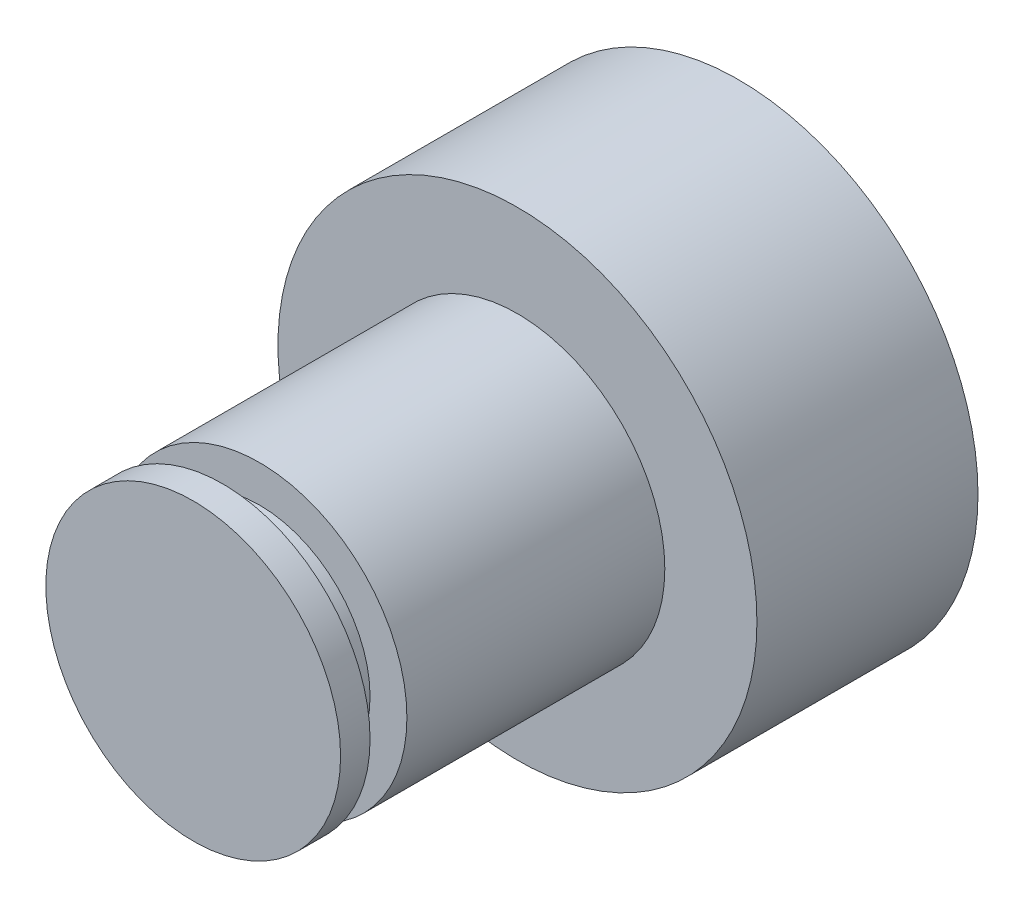
SolidWorks part; units mm, degrees
ref_plane "Front Plane" through (0, 0, 0) normal (0, 0, 1) x (1, 0, 0)
ref_plane "Top Plane" through (0, 0, 0) normal (0, 1, 0) x (1, 0, 0)
ref_plane "Right Plane" through (0, 0, 0) normal (1, 0, 0) x (0, 0, -1)
sketch "Sketch1" plane through (0, 0, 0) normal (0, 0, 1) x (1, 0, 0)
  circle A0 centre (0, 0) radius 6.5
  dimension "D1" = 13
extrude "Boss-Extrude1" add sketch "Sketch1" against normal blind 6
sketch "Sketch2" plane through (0, 0, 0) normal (0, 0, 1) x (1, 0, 0)
  circle A0 centre (0, 0) radius 4
extrude "Boss-Extrude2" add sketch "Sketch2" along normal blind 8.8
ref_plane "Plane1" through (0, 0, 7.5) normal (0, 0, 1) x (1, 0, 0)
sketch "Sketch3" plane through (0, 0, 7.5) normal (0, 0, 1) x (1, 0, 0)
  circle A0 centre (0, 0) radius 3
  circle A1 centre (0, 0) radius 4
extrude "Cut-Extrude1" cut sketch "Sketch3" against normal mid plane 1
equation "\"diameter\"=13"
equation "\"D1@Sketch1\"=\"diameter\""
